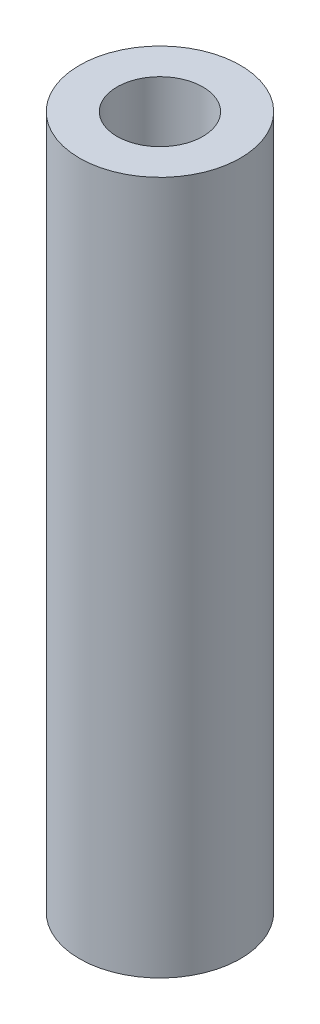
SolidWorks part; units mm, degrees
ref_plane "Top Plane" through (0, 0, 0) normal (0, 0, 1) x (1, 0, 0)
ref_plane "Front Plane" through (0, 0, 0) normal (0, 1, 0) x (1, 0, 0)
ref_plane "Right Plane" through (0, 0, 0) normal (1, 0, 0) x (0, 0, -1)
sketch "Profile Sketch" plane through (0, 0, 0) normal (0, 1, 0) x (1, 0, 0)
  circle A0 centre (0, 0) radius 1.6
  circle A1 centre (0, 0) radius 3
  dimension "D1" = 3.2
  dimension "D2" = 6
extrude "Profile Extrude" add sketch "Profile Sketch" along normal blind 25.8572
